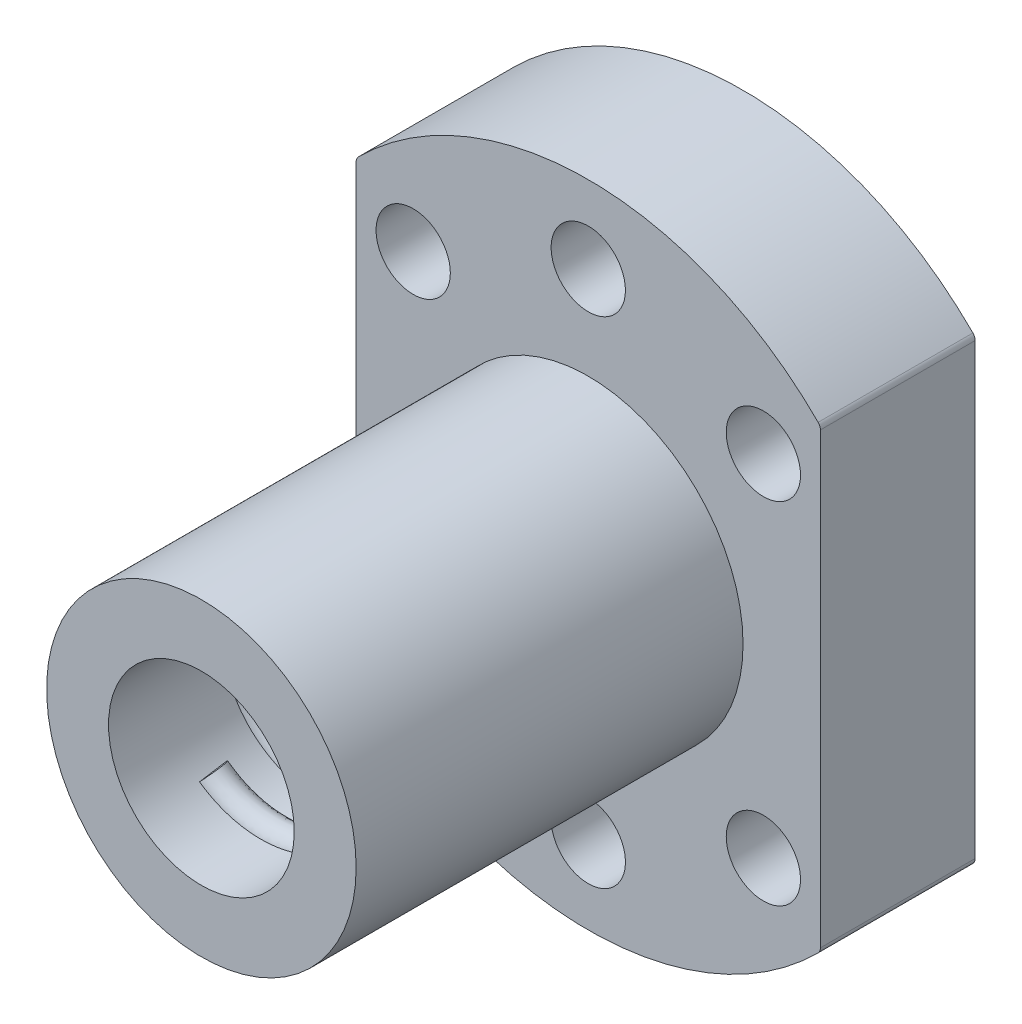
SolidWorks part; units mm, degrees
ref_plane "Front Plane" through (0, 0, 0) normal (0, 0, 1) x (1, 0, 0)
ref_plane "Top Plane" through (0, 0, 0) normal (0, 1, 0) x (1, 0, 0)
ref_plane "Right Plane" through (0, 0, 0) normal (1, 0, 0) x (0, 0, -1)
sketch "Sketch1" plane through (0, 0, 0) normal (0, 0, 1) x (1, 0, 0)
  line L0 (0, -30.3373) -> (0, 30.3373) construction
  line L1 (-31.8597, 0) -> (31.8597, 0) construction
  line L2 (-11.3137, 11.3137) -> (0, 0) construction
  line L3 (0, 0) -> (11.3137, 11.3137) construction
  line L4 (-15, 14.6969) -> (-15, -14.6969)
  line L5 (15, 14.6969) -> (15, -14.6969)
  circle A0 centre (0, 0) radius 6
  circle A1 centre (0, 0) radius 16 construction
  arc A2 (-15, -14.6969) -> (15, -14.6969) centre (0, 0) ccw
  circle A3 centre (0, 16) radius 2.4
  circle A4 centre (-11.3137, 11.3137) radius 2.4
  circle A5 centre (11.3137, 11.3137) radius 2.4
  circle A6 centre (11.3137, -11.3137) radius 2.4
  circle A7 centre (0, -16) radius 2.4
  circle A8 centre (-11.3137, -11.3137) radius 2.4
  arc A9 (15, 14.6969) -> (-15, 14.6969) centre (0, 0) ccw
  point P4 (0, 0)
  point P8 (0, 0)
  dimension "D1" = 12
  dimension "D2" = 32
  dimension "D3" = 42
  dimension "D4" = 4.8
  dimension "D5" = 45
  dimension "D6" = 45
  dimension "D7" = 15
extrude "Boss-Extrude1" add sketch "Sketch1" along normal blind 10
sketch "Sketch2" plane through (0, 0, 10) normal (0, 0, 1) x (1, 0, 0)
  circle A0 centre (0, 0) radius 10
  circle A1 centre (0, 0) radius 6 construction
  circle A2 centre (0, 0) radius 6
  dimension "D1" = 20
extrude "Boss-Extrude2" add sketch "Sketch2" along normal blind 25
ref_plane "Plane1" through (0, 0, 10) normal (0, 0, 1) x (1, 0, 0)
sketch "Sketch3" plane through (0, 0, 10) normal (0, 0, 1) x (1, 0, 0)
  circle A0 centre (0, 0) radius 6 construction
  circle A1 centre (0, 0) radius 6
curve "Helix/Spiral1" pitch 4 height 20 turns 5
ref_plane "Plane2" through (-4.2426, -4.2426, 10) normal (0.7032, -0.7032, -0.1055) x (-0.0746, 0.0746, -0.9944)
sketch "Sketch6" plane through (-4.2426, -4.2426, 10) normal (0.7032, -0.7032, -0.1055) x (-0.0746, 0.0746, -0.9944)
  line L0 (0, 0) -> (0, 0.4305) construction
  line L1 (0, 0) -> (0.3145, 0) construction
  line L2 (0, 0) -> (0, -0.3652) construction
  circle A0 centre (0, -0.3) radius 1
  dimension "D1" = 2
  dimension "D2" = 0.3
sweep "Sweep1" add profiles "Sketch6" path "Helix/Spiral1"
fillet "Fillet1" radius 0.5 4 edges at (-15, 14.6969, 5) (-15, -14.6969, 5) (15, -14.6969, 5) (15, 14.6969, 5)
